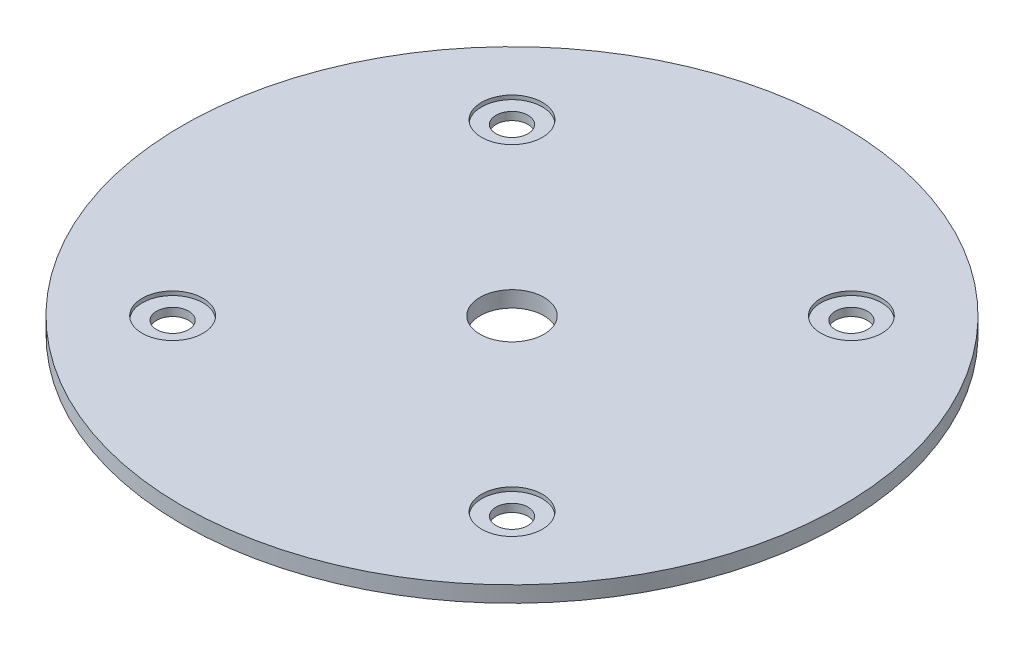
SolidWorks part; units mm, degrees
ref_plane "Front Plane" through (0, 0, 0) normal (0, 0, 1) x (1, 0, 0)
ref_plane "Top Plane" through (0, 0, 0) normal (0, 1, 0) x (1, 0, 0)
ref_plane "Right Plane" through (0, 0, 0) normal (1, 0, 0) x (0, 0, -1)
sketch "Sketch2" plane through (0, 0, 0) normal (0, 1, 0) x (1, 0, 0)
  circle A0 centre (0, 0) radius 65.405
  dimension "D1" = 130.81
extrude "Boss-Extrude1" add sketch "Sketch2" along normal mid plane 3.175
sketch "Sketch3" plane through (0, 1.5875, 0) normal (0, 1, 0) x (1, 0, 0)
  line L0 (-1000, 0) -> (49000, 0) construction
  line L1 (-33.676, -33.676) -> (33.676, 33.676) construction
  line L2 (33.676, 33.676) -> (0, 0) construction
  line L3 (-33.676, 33.676) -> (33.676, -33.676) construction
  point P9 (0, 0)
  point P19 (-33.676, 33.676)
  point P22 (33.676, 33.676)
  point P25 (33.676, -33.676)
  point P28 (-33.676, -33.676)
  dimension "D1" = 45
  dimension "D2" = 95.25
hole_wizard "1/4 (0.25) Diameter Hole1" positions "Sketch3" profile "Sketch7" hole size "1/4" standard "ANSI Inch"
sketch "Sketch7" plane through (-33.676, 1.5875, 33.676) normal (1, 0, 0) x (0, 0, 1)
  line L0 (0, 0) -> (0, 3.175)
  line L1 (0, 3.175) -> (3.175, 3.175)
  line L2 (3.175, 3.175) -> (3.175, 0)
  line L5 (3.175, 0) -> (0, 0)
  line L11 (0, -6.35) -> (0, 107.95) construction
  dimension "Thru Hole Dia." = 6.35
  dimension "Thru Hole Depth" = 3.175
sketch "Sketch8" plane through (0, 1.5875, 0) normal (0, 1, 0) x (1, 0, 0)
  point P0 (0, 0)
hole_wizard "1/2 (0.5) Diameter Hole1" positions "Sketch8" profile "Sketch9" hole size "1/2" standard "ANSI Inch" end condition through all
sketch "Sketch9" plane through (0, 1.5875, 0) normal (1, 0, 0) x (0, 0, 1)
  line L0 (0, 0) -> (0, 3.175)
  line L1 (0, 3.175) -> (6.35, 3.175)
  line L2 (6.35, 3.175) -> (6.35, 0)
  line L5 (6.35, 0) -> (0, 0)
  line L11 (0, -6.35) -> (0, 107.95) construction
  dimension "Thru Hole Dia." = 12.7
  dimension "Thru Hole Depth" = 3.175
sketch "Sketch10" plane through (0, 1.5875, 0) normal (0, 1, 0) x (1, 0, 0)
  circle A0 centre (-33.676, 33.676) radius 6.0325
  circle A1 centre (33.676, 33.676) radius 6.0325
  circle A2 centre (33.676, -33.676) radius 6.0325
  circle A3 centre (-33.676, -33.676) radius 6.0325
  dimension "D1" = 12.065
extrude "Cut-Extrude1" cut sketch "Sketch10" against normal blind 0.7937
mirror "Mirror1" about plane through (0, 0, 0) normal (0, 1, 0) of "Cut-Extrude1"
equation "\"AIRFRAME_OD\"= 5.15in"
equation "\"AIRFRAME_ID\"= 5.00in"
equation "\"FLAT_T\"= 0.125in"
equation "\"NOSE_EXP_L\"= 27in"
equation "\"NOSE_SHOULDER_L\"= 5in"
equation "\"MAIN_L\"= 30in"
equation "\"RECO_COUP_L\"= 10in"
equation "\"RECO_SWITCH_L\"= 2in"
equation "\"DROGUE_L\"= 20in"
equation "\"ATS_FORE_COUP_L\"= 5.5in"
equation "\"ATS_AFT_COUP_L\"= 4.5in"
equation "\"LOWER_L\"= 30in"
equation "\"FIN_N\"= 4"
equation "\"CR_AFT_X\"= 0.5in"
equation "\"CR_FORE_X\"= 9.25in"
equation "\"D1@Sketch2\"=\"AIRFRAME_OD\""
equation "\"D1@Boss-Extrude1\"=\"FLAT_T\""
equation "\"COUPLER_OD\"= 4.998in"
equation "\"COUPLER_ID\"= 4.88in"
equation "\"RECO_ROD_X\"= 3.5in"
equation "\"ATS_ROD_X\"= 3.75in"
equation "\"FIN_ROOT\"= 8in"
equation "\"FIN_X\"= 0.75in"
equation "\"MOTOR_OD\"= 3.091in"
equation "\"MOTOR_ID\"= 3.00in"
equation "\"MOTOR_L\"= 14in"
equation "\"MOTOR_LOWER_X\"= 2in"
equation "\"D2@Sketch3\"=\"ATS_ROD_X\""
